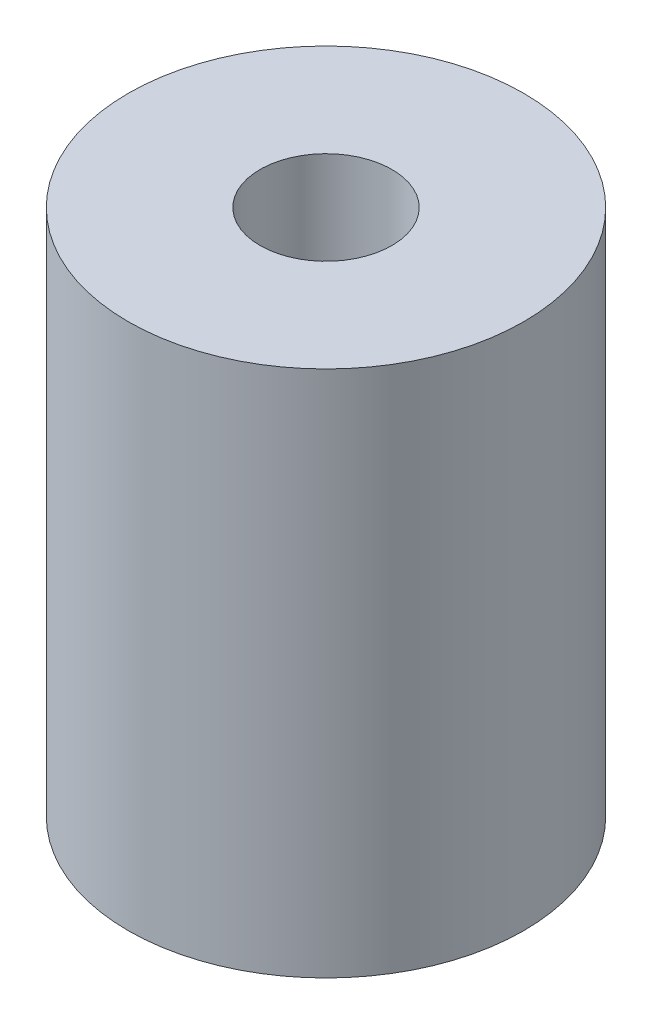
SolidWorks part; units mm, degrees
material "ABS"
ref_plane "Front Plane" through (0, 0, 0) normal (0, 0, 1) x (1, 0, 0)
ref_plane "Top Plane" through (0, 0, 0) normal (0, 1, 0) x (1, 0, 0)
ref_plane "Right Plane" through (0, 0, 0) normal (1, 0, 0) x (0, 0, -1)
sketch "Sketch1" plane through (0, 0, 0) normal (0, 1, 0) x (1, 0, 0)
  circle A0 centre (0, 0) radius 3.175
  circle A1 centre (0, 0) radius 9.525
  dimension "D1" = 6.35
  dimension "D2" = 19.05
extrude "Boss-Extrude1" add sketch "Sketch1" along normal blind 25.4
